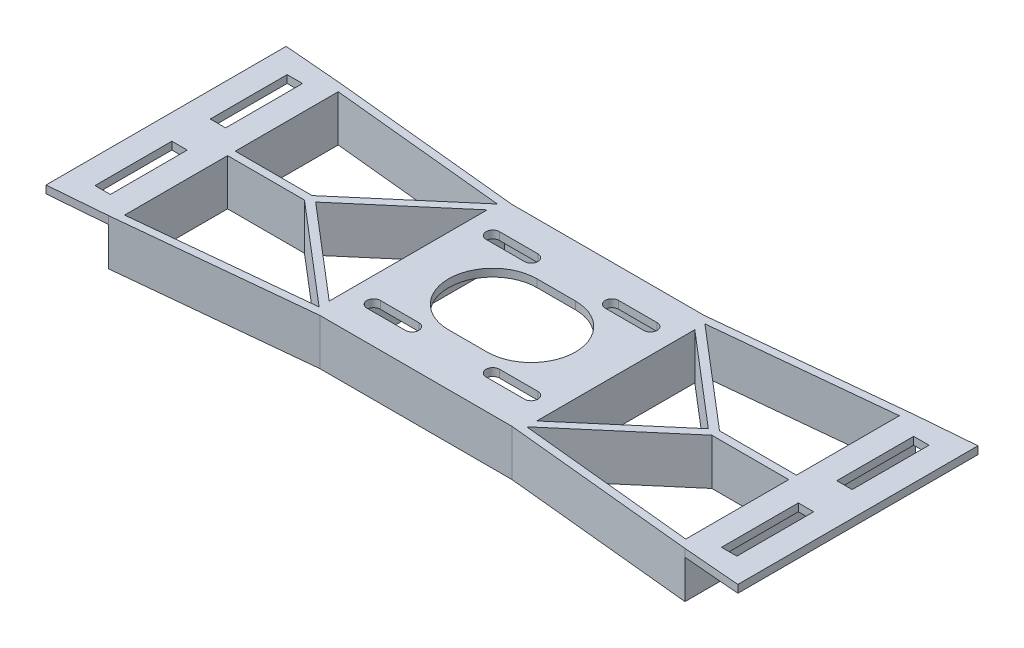
SolidWorks part; units mm, degrees
ref_plane "Front Plane" through (0, 0, 0) normal (0, 0, 1) x (1, 0, 0)
ref_plane "Top Plane" through (0, 0, 0) normal (0, 1, 0) x (1, 0, 0)
ref_plane "Right Plane" through (0, 0, 0) normal (1, 0, 0) x (0, 0, -1)
sketch "Sketch1" plane through (0, 0, 0) normal (0, 1, 0) x (1, 0, 0)
  line L0 (0, 0) -> (31, 0) construction
  line L1 (0, 0) -> (0, 31) construction
  line L2 (0, 31) -> (31, 31) construction
  line L3 (31, 31) -> (31, 0) construction
  line L4 (5, 32.75) -> (-5, 32.75)
  line L5 (-5, 29.25) -> (5, 29.25)
  line L6 (26, 29.25) -> (36, 29.25)
  line L7 (36, 32.75) -> (26, 32.75)
  line L8 (-5, 1.75) -> (5, 1.75)
  line L9 (5, -1.75) -> (-5, -1.75)
  line L10 (26, -1.75) -> (36, -1.75)
  line L11 (36, 1.75) -> (26, 1.75)
  line L12 (0, 31) -> (31, 0) construction
  line L13 (-14.0987, 27) -> (46.8393, 27) construction
  line L14 (100.5, 40.5) -> (-69.5, 40.5)
  line L15 (100.5, 40.5) -> (100.5, -9.5)
  line L16 (100.5, -9.5) -> (-69.5, -9.5)
  line L17 (-69.5, 40.5) -> (-69.5, -9.5)
  line L18 (-14.0987, 4) -> (46.8393, 4) construction
  line L19 (20.5, 31) -> (20.5, 0) construction
  line L20 (10.5, 31) -> (10.5, 0) construction
  line L21 (10.5, 27) -> (20.5, 27)
  line L22 (10.5, 4) -> (20.5, 4)
  arc A0 (10.5, 27) -> (10.5, 4) centre (10.5, 15.5) ccw
  arc A1 (5, 32.75) -> (5, 29.25) centre (5, 31) cw
  arc A2 (26, 32.75) -> (26, 29.25) centre (26, 31) ccw
  arc A3 (5, 1.75) -> (5, -1.75) centre (5, 0) cw
  arc A4 (26, 1.75) -> (26, -1.75) centre (26, 0) ccw
  arc A5 (-5, -1.75) -> (-5, 1.75) centre (-5, 0) cw
  arc A6 (36, -1.75) -> (36, 1.75) centre (36, 0) ccw
  arc A7 (36, 32.75) -> (36, 29.25) centre (36, 31) cw
  arc A8 (-5, 29.25) -> (-5, 32.75) centre (-5, 31) cw
  arc A9 (20.5, 27) -> (20.5, 4) centre (20.5, 15.5) cw
  point P41 (15.5, 15.5)
  dimension "D23" = 23
  dimension "D20" = 1.75
  dimension "D22" = 1.75
  dimension "D28" = 10
  dimension "D1" = 31
  dimension "D2" = 31
  dimension "D3" = 10
  dimension "D4" = 10
  dimension "D5" = 10
  dimension "D6" = 10
  dimension "D7" = 10
  dimension "D8" = 10
  dimension "D9" = 10
  dimension "D10" = 10
  dimension "D11" = 5
  dimension "D12" = 5
  dimension "D13" = 5
  dimension "D14" = 5
  dimension "D15" = 5
  dimension "D16" = 5
  dimension "D17" = 5
  dimension "D18" = 5
  dimension "D19" = 3.5
  dimension "D21" = 1.75
  dimension "D24" = 170
  dimension "D25" = 4
  dimension "D26" = 50
  dimension "D27" = 5
extrude "Boss-Extrude1" add sketch "Sketch1" along normal blind 2
sketch "Sketch2" plane through (0, 0, 0) normal (0, -1, 0) x (-1, 0, 0)
  line L0 (69.5, -9.5) -> (-100.5, -9.5) construction
  line L1 (61.5, -9.5) -> (59.5, -9.5)
  line L2 (61.5, -9.5) -> (61.5, 40.5)
  line L3 (61.5, 40.5) -> (59.5, 40.5)
  line L4 (59.5, -9.5) -> (59.5, 40.5)
  line L5 (-100.5, 40.5) -> (69.5, 40.5) construction
  line L7 (-90.5, -9.5) -> (-92.5, -9.5)
  line L8 (-90.5, -9.5) -> (-90.5, 40.5)
  line L9 (-90.5, 40.5) -> (-92.5, 40.5)
  line L10 (-92.5, -9.5) -> (-92.5, 40.5)
  line L11 (69.5, 40.5) -> (69.5, -9.5) construction
  line L12 (-100.5, -9.5) -> (-100.5, 40.5) construction
  dimension "D1" = 2
  dimension "D2" = 2
  dimension "D3" = 10
  dimension "D4" = 10
extrude "Boss-Extrude2" add sketch "Sketch2" along normal blind 10
sketch "Sketch3" plane through (0, 0, 0) normal (0, -1, 0) x (-1, 0, 0)
  line L0 (-90.5, -9.5) -> (-90.5, 40.5) construction
  line L1 (59.5, 40.5) -> (-90.5, 40.5)
  line L2 (59.5, 40.5) -> (59.5, 38.5)
  line L3 (59.5, 38.5) -> (-90.5, 38.5)
  line L4 (-90.5, 40.5) -> (-90.5, 38.5)
  line L6 (59.5, -9.5) -> (-90.5, -9.5)
  line L7 (59.5, -9.5) -> (59.5, -7.5)
  line L8 (59.5, -7.5) -> (-90.5, -7.5)
  line L9 (-90.5, -9.5) -> (-90.5, -7.5)
  dimension "D1" = 2
  dimension "D2" = 2
extrude "Boss-Extrude3" add sketch "Sketch3" along normal blind 10
sketch "Sketch4" plane through (0, 2, 0) normal (0, 1, 0) x (1, 0, 0)
  line L0 (15.5, 40.5) -> (15.5, -9.5) construction
  line L1 (100.5, 40.5) -> (-69.5, 40.5) construction
  line L2 (-69.5, -9.5) -> (100.5, -9.5) construction
  line L3 (-9.5, 40.5) -> (-9.5, -9.5) construction
  line L4 (40.5, 40.5) -> (40.5, -9.5) construction
  line L6 (-69.5, -9.5) -> (-9.5, -9.5)
  line L7 (-69.5, -9.5) -> (-69.5, 40.5)
  line L8 (-69.5, 40.5) -> (-9.5, 40.5)
  line L9 (-9.5, -9.5) -> (-9.5, 40.5)
  dimension "D1" = 25
  dimension "D2" = 25
extrude "Cut-Extrude2" cut sketch "Sketch4" against normal through all
ref_plane "Plane1" through (15.5, 0, 0) normal (-1, 0, 0) x (0, 0, 1)
mirror "Mirror1" about plane through (15.5, 0, 0) normal (-1, 0, 0) of "Cut-Extrude2"
sketch "Sketch5" plane through (0, 2, 0) normal (0, 1, 0) x (1, 0, 0)
  line L0 (-9.5, 15.5) -> (-59.5, 15.5) construction
  line L1 (-9.5, -9.5) -> (-9.5, 40.5) construction
  line L2 (40.5, 15.5) -> (90.5, 15.5) construction
  line L3 (40.5, -9.5) -> (40.5, 40.5) construction
  line L4 (-59.5, 15.5) -> (-59.5, 45.5) construction
  line L5 (-59.5, 15.5) -> (-59.5, -14.5) construction
  line L6 (90.5, 15.5) -> (90.5, 45.5) construction
  line L7 (90.5, 15.5) -> (90.5, -14.5) construction
  line L8 (40.5, 40.5) -> (90.5, 45.5)
  line L9 (90.5, 45.5) -> (90.5, -14.5)
  line L10 (90.5, -14.5) -> (40.5, -9.5)
  line L11 (40.5, 40.5) -> (40.5, 38.5)
  line L12 (40.5, 38.5) -> (40.5, -7.69)
  line L13 (42.5, 38.69) -> (68.4917, 16.5)
  line L14 (68.4917, 16.5) -> (88.5, 16.5)
  line L15 (88.5, 14.5) -> (68.4917, 14.5)
  line L16 (68.4917, 14.5) -> (42.5, -7.69)
  line L17 (40.5, -7.69) -> (40.5, -9.5)
  line L19 (88.5, 14.5) -> (88.5, -12.29)
  line L20 (88.5, -12.29) -> (42.5, -7.69)
  line L21 (88.5, 16.5) -> (88.5, 18.0803)
  line L22 (88.5, 43.29) -> (42.5, 38.69)
  line L23 (88.5, 18.0803) -> (88.5, 43.29)
  line L24 (66.5827, 15.5) -> (42.5, 36.0603)
  line L25 (42.5, 36.0603) -> (42.5, -5.0603)
  line L26 (42.5, -5.0603) -> (66.5827, 15.5)
  dimension "D1" = 50
  dimension "D2" = 50
  dimension "D3" = 30
  dimension "D4" = 2
  dimension "D5" = 2
  dimension "D6" = 2
  dimension "D7" = 2
  dimension "D8" = 2
  dimension "D9" = 46
  dimension "D10" = 2
  dimension "D11" = 2
  dimension "D12" = 1
  dimension "D13" = 1
extrude "Boss-Extrude5" add sketch "Sketch5" against normal blind 12
sketch "Sketch7" plane through (0, 2, 0) normal (0, 1, 0) x (1, 0, 0)
  line L0 (90.5, -14.5) -> (105.5, -15.7408)
  line L1 (90.5, 45.5) -> (105.5, 46.7408)
  line L2 (105.5, 46.7408) -> (105.5, -15.7408)
  line L3 (90.5, -14.5) -> (90.5, 45.5)
  dimension "D1" = 15
extrude "Boss-Extrude7" add sketch "Sketch7" against normal blind 2
sketch "Sketch8" plane through (0, 2, 0) normal (0, 1, 0) x (1, 0, 0)
  line L0 (105.5, 15.5) -> (88.5, 15.5) construction
  line L1 (105.5, -15.7408) -> (105.5, 46.7408) construction
  line L3 (95, 10.5) -> (99, 10.5)
  line L4 (95, 10.5) -> (95, -9.5)
  line L5 (95, -9.5) -> (99, -9.5)
  line L6 (99, 10.5) -> (99, -9.5)
  line L7 (99, 20.5) -> (95, 20.5)
  line L8 (99, 20.5) -> (99, 40.5)
  line L9 (99, 40.5) -> (95, 40.5)
  line L10 (95, 20.5) -> (95, 40.5)
  dimension "D1" = 20
  dimension "D2" = 20
  dimension "D3" = 4
  dimension "D4" = 4
  dimension "D5" = 5
  dimension "D6" = 5
  dimension "D7" = 6.5
  dimension "D8" = 6.5
extrude "Cut-Extrude3" cut sketch "Sketch8" against normal blind 2
mirror "Mirror2" about plane through (15.5, 0, 0) normal (-1, 0, 0) of "Boss-Extrude7", "Boss-Extrude5", "Cut-Extrude3"
